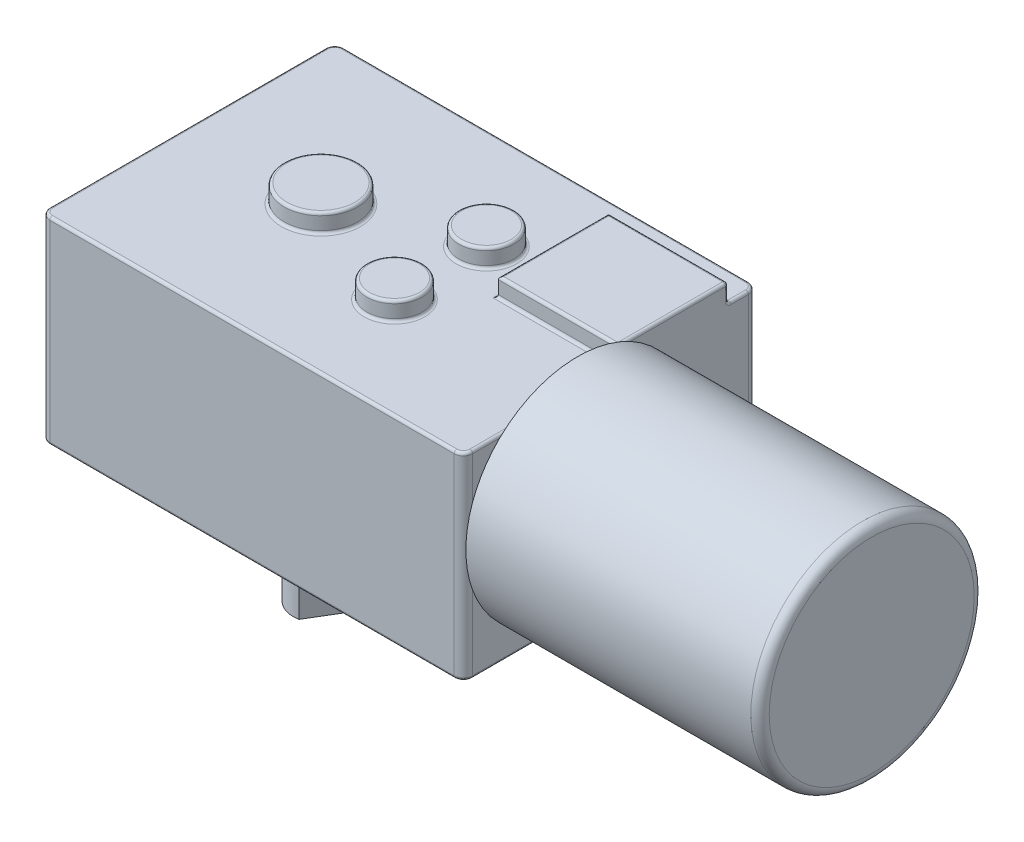
SolidWorks part; units mm, degrees
ref_plane "Front Plane" through (0, 0, 0) normal (0, 0, 1) x (1, 0, 0)
ref_plane "Top Plane" through (0, 0, 0) normal (0, 1, 0) x (1, 0, 0)
ref_plane "Right Plane" through (0, 0, 0) normal (1, 0, 0) x (0, 0, -1)
sketch "Sketch1" plane through (0, 0, 0) normal (0, 1, 0) x (1, 0, 0)
  line L1 (-23, 16) -> (23, 16)
  line L2 (-23, 16) -> (-23, -16)
  line L3 (-23, -16) -> (23, -16)
  line L4 (23, 16) -> (23, -16)
  line L5 (-23, 16) -> (23, -16) construction
  line L6 (-23, -16) -> (23, 16) construction
  point P0 (0, 0)
  dimension "D1" = 32
  dimension "D2" = 46
extrude "Boss-Extrude1" add sketch "Sketch1" along normal blind 21.5
fillet "Fillet1" radius 1 4 edges at (-23, 10.75, -16) (-23, 10.75, 16) (23, 10.75, -16) (23, 10.75, 16)
sketch "Sketch2" plane through (0, 21.5, 0) normal (0, 1, 0) x (1, 0, 0)
  line L0 (23, -15) -> (23, 15) construction
  line L1 (23, 12.8) -> (10, 12.8)
  line L2 (23, 12.8) -> (23, 0.8)
  line L3 (23, 0.8) -> (10, 0.8)
  line L4 (10, 12.8) -> (10, 0.8)
  line L5 (22, 16) -> (-22, 16) construction
  dimension "D1" = 3.2
  dimension "D2" = 12
  dimension "D3" = 13
extrude "Boss-Extrude2" add sketch "Sketch2" along normal blind 2
sketch "Sketch3" plane through (0, 21.5, 0) normal (0, 1, 0) x (1, 0, 0)
  line L0 (-23, 0) -> (-8.5, 0) construction
  line L1 (-23, 15) -> (-23, -15) construction
  line L3 (-8.5, 0) -> (4.5, 0) construction
  line L4 (4.5, 0) -> (4.5, 5) construction
  line L5 (4.5, 0) -> (4.5, -5) construction
  circle A0 centre (-8.5, 0) radius 4
  circle A1 centre (4.5, 5) radius 3
  circle A2 centre (4.5, -5) radius 3
  dimension "D2" = 8
  dimension "D3" = 6
  dimension "D4" = 6
  dimension "D1" = 14.5
  dimension "D5" = 13
  dimension "D6" = 5
  dimension "D7" = 5
extrude "Boss-Extrude3" add sketch "Sketch3" along normal blind 2
sketch "Sketch4" plane through (0, 0, 0) normal (0, -1, 0) x (1, 0, 0)
  line L0 (-23, 0) -> (-8.5, 0) construction
  line L1 (-23, -15) -> (-23, 15) construction
  line L2 (-16.4, 9.4) -> (16.4, 9.4) construction
  line L3 (16.4, 9.4) -> (16.4, -9.4) construction
  line L4 (16.4, -9.4) -> (-16.4, -9.4) construction
  line L5 (-16.4, -9.4) -> (-16.4, 9.4) construction
  line L6 (-22, 16) -> (22, 16) construction
  line L7 (23, 15) -> (23, -15) construction
  line L8 (22, -16) -> (-22, -16) construction
  circle A0 centre (-8.5, 0) radius 6.75
  circle A1 centre (-16.4, 9.4) radius 4
  circle A2 centre (-16.4, 9.4) radius 1.5
  circle A3 centre (-16.4, -9.4) radius 4
  circle A4 centre (-16.4, -9.4) radius 1.5
  circle A6 centre (16.4, -9.4) radius 1.5
  circle A7 centre (16.4, -9.4) radius 4
  circle A8 centre (16.4, 9.4) radius 1.5
  circle A9 centre (16.4, 9.4) radius 4
  circle A10 centre (4.5, 5) radius 3
  circle A11 centre (4.5, -5) radius 3
  point P29 (0, 0)
  dimension "D2" = 13.5
  dimension "D7" = 3
  dimension "D8" = 8
  dimension "D9" = 8
  dimension "D10" = 3
  dimension "D11" = 3
  dimension "D12" = 8
  dimension "D13" = 3
  dimension "D14" = 8
  dimension "D1" = 14.5
  dimension "D3" = 6.6
  dimension "D4" = 6.6
  dimension "D5" = 6.6
  dimension "D6" = 6.6
  dimension "D15" = 18.8
  dimension "D16" = 32.8
  dimension "D17" = 7.9
extrude "Boss-Extrude4" add sketch "Sketch4" along normal blind 2
fillet "Fillet2" radius 0.3 49 edges at (23, 22.5, -0.8) (23, 22.5, -12.8) (4.5, 23.5, 8) (16.5, 23.5, -0.8) (10, 23.5, -6.8) (16.5, 23.5, -12.8) (23, 23.5, -6.8) (4.5, 23.5, -2) (-8.5, 23.5, 4) (-16.4, -2, -10.9) (-16.4, -2, -13.4) (16.4, -2, -10.9) (16.4, -2, -13.4) (16.4, -2, 7.9) (16.4, -2, 5.4) (4.5, -2, -8) (4.5, -2, 2) (-16.4, -2, 7.9) (-16.4, -2, 5.4) (-22.7071, 0, 15.7071) (0, 0, 16) (22.7071, 0, 15.7071) (23, 0, 0) (22.7071, 0, -15.7071) (0, 0, -16) (-22.7071, 0, -15.7071) (-23, 0, 0) (-8.5, 0, -6.75) (-16.4, 0, 13.4) (-16.4, 0, -5.4) (16.4, 0, -5.4) (16.4, 0, 13.4) (4.5, 0, 8) (4.5, 0, -2) (23, 21.5, 7.1) (22.7071, 21.5, 15.7071) (0, 21.5, 16) (-22.7071, 21.5, 15.7071) (-23, 21.5, 0) (-22.7071, 21.5, -15.7071) (0, 21.5, -16) (22.7071, 21.5, -15.7071) (23, 21.5, -13.9) (16.5, 21.5, -12.8) (10, 21.5, -6.8) (16.5, 21.5, -0.8) (-8.5, 21.5, 4) (4.5, 21.5, -2) (4.5, 21.5, 8)
sketch "Sketch5" plane through (23, 0, 0) normal (1, 0, 0) x (0, 0, -1)
  line L0 (-3.584, 12.5) -> (0, 12.5) construction
  line L1 (0, 12.5) -> (0, 0) construction
  circle A0 centre (-3.584, 12.5) radius 12.15
  dimension "D1" = 24.3
  dimension "D2" = 12.5
extrude "Boss-Extrude5" add sketch "Sketch5" along normal blind 32
fillet "Fillet3" radius 1 1 edges at (55, 12.5, -8.566)
sketch "Sketch6" plane through (0, -2, 0) normal (0, 1, 0) x (1, 0, 0)
  circle A0 centre (-8.5, 0) radius 5
  dimension "D1" = 10
extrude "Cut-Extrude1" cut sketch "Sketch6" along normal blind 0.1
sketch "Sketch7" plane through (0, -1.9, 0) normal (0, -1, 0) x (1, 0, 0)
  circle A1 centre (-8.5, 0) radius 3
extrude "Boss-Extrude6" add sketch "Sketch7" along normal blind 14
sketch "Sketch8" plane through (0, -15.9, 0) normal (0, -1, 0) x (1, 0, 0)
  line L0 (-7.9392, 2.9471) -> (-5.6334, -0.8848)
  line L1 (-7.9392, 2.9471) -> (-4.6301, 4.9384)
  line L2 (-5.6334, -0.8848) -> (-2.3243, 1.1065)
  line L3 (-4.6301, 4.9384) -> (-2.3243, 1.1065)
  circle A0 centre (-8.5, 0) radius 3 construction
  circle A1 centre (-8.5, 0) radius 3 construction
  dimension "D1" = 2
extrude "Cut-Extrude2" cut sketch "Sketch8" against normal blind 11
